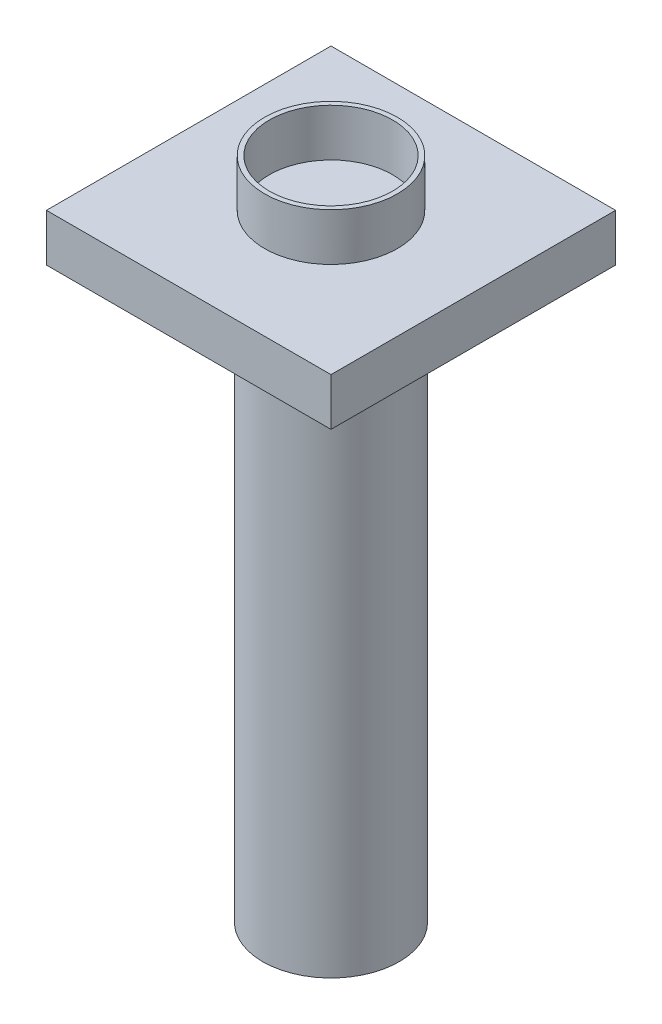
SolidWorks part; units mm, degrees
ref_plane "Front Plane" through (0, 0, 0) normal (0, 0, 1) x (1, 0, 0)
ref_plane "Top Plane" through (0, 0, 0) normal (0, 1, 0) x (1, 0, 0)
ref_plane "Right Plane" through (0, 0, 0) normal (1, 0, 0) x (0, 0, -1)
sketch "Sketch1" plane through (0, 0, 0) normal (0, 1, 0) x (1, 0, 0)
  circle A0 centre (0, 0) radius 72
  dimension "D1" = 144
extrude "Boss-Extrude1" add sketch "Sketch1" along normal blind 600
sketch "Sketch2" plane through (0, 600, 0) normal (0, 1, 0) x (1, 0, 0)
  line L1 (-150, -150) -> (150, -150)
  line L2 (-150, -150) -> (-150, 150)
  line L3 (-150, 150) -> (150, 150)
  line L4 (150, -150) -> (150, 150)
  line L5 (-150, -150) -> (150, 150) construction
  line L6 (-150, 150) -> (150, -150) construction
  point P0 (0, 0)
  dimension "D1" = 300
  dimension "D2" = 300
extrude "Boss-Extrude2" add sketch "Sketch2" along normal blind 50
sketch "Sketch3" plane through (0, 650, 0) normal (0, 1, 0) x (1, 0, 0)
  circle A0 centre (0, 0) radius 70
  circle A1 centre (0, 0) radius 65
  dimension "D1" = 130
extrude "Boss-Extrude3" add sketch "Sketch3" along normal blind 50
